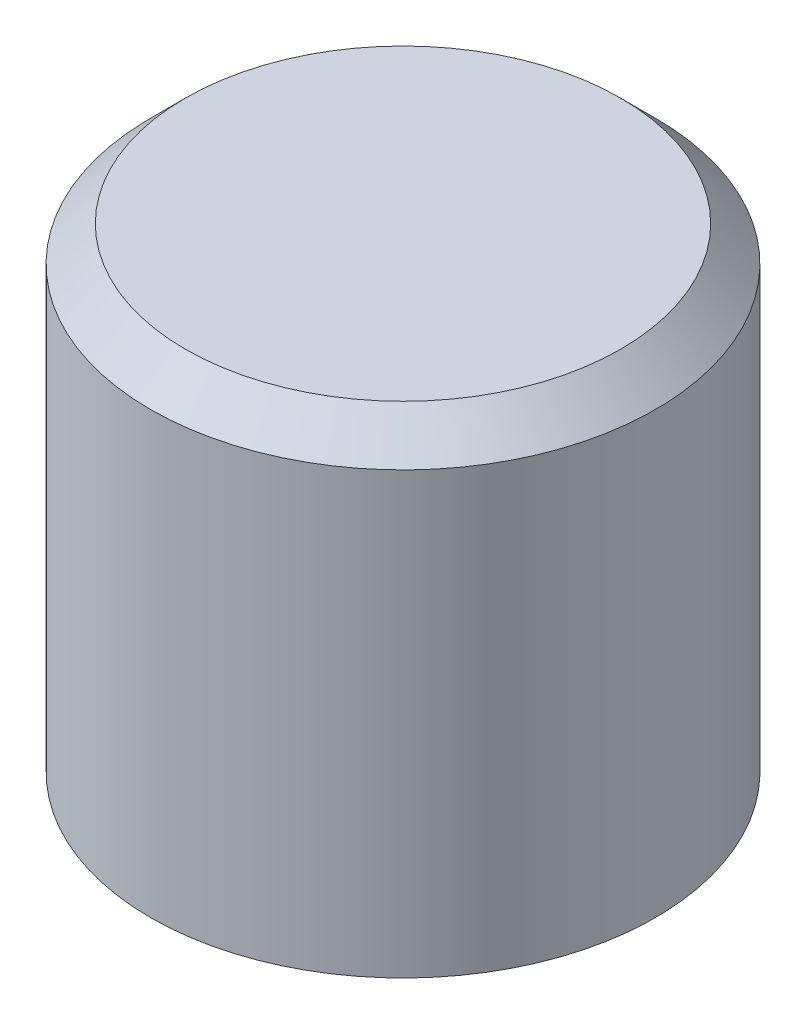
SolidWorks part; units mm, degrees
ref_plane "Front Plane" through (0, 0, 0) normal (0, 0, 1) x (1, 0, 0)
ref_plane "Top Plane" through (0, 0, 0) normal (0, 1, 0) x (1, 0, 0)
ref_plane "Right Plane" through (0, 0, 0) normal (1, 0, 0) x (0, 0, -1)
sketch "Sketch1" plane through (0, 0, 0) normal (0, 1, 0) x (1, 0, 0)
  line L0 (0, 69.551) -> (0, 0) construction
  line L1 (0, 0) -> (72.1805, 0) construction
  circle A0 centre (0, 0) radius 3.625
  dimension "D1" = 7.25
extrude "Boss-Extrude1" add sketch "Sketch1" along normal blind 6.82
chamfer "Chamfer1" distance 0.5 angle 45 1 edges at (0, 6.82, 3.625)
sketch "Sketch2" plane through (0, 0, 0) normal (0, -1, 0) x (1, 0, 0)
  line L0 (0, 5.8745) -> (0, 0) construction
  line L1 (0, 0) -> (6.4339, 0) construction
  line L2 (-1.6, 1.6) -> (1.6, 1.6)
  line L3 (1.6, 1.6) -> (1.6, -1.6)
  line L4 (-1.6, -1.6) -> (1.6, -1.6)
  line L5 (-1.6, 1.6) -> (-1.6, -1.6)
  point P8 (1.6, 0)
  point P10 (0, -1.6)
  point P11 (0, 1.6)
  dimension "D1" = 3.2
  dimension "D2" = 3.2
extrude "Cut-Extrude1" cut sketch "Sketch2" against normal offset from surface (2.93 mm away) 3.89 up to face at (0, 6.82, 3.125)
